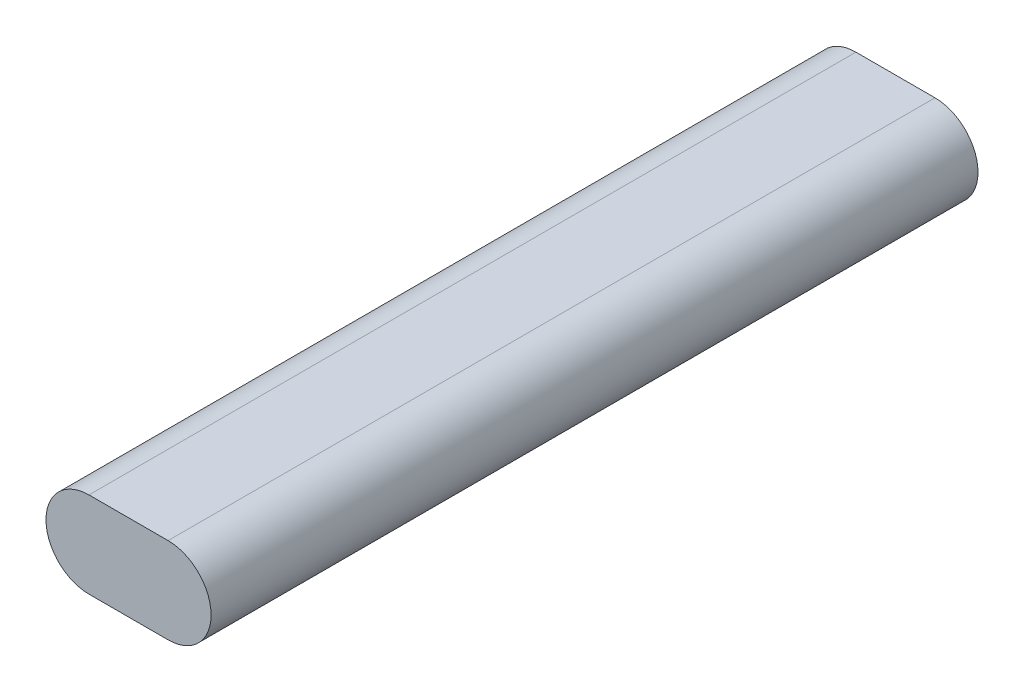
SolidWorks part; units mm, degrees
ref_plane "Front Plane" through (0, 0, 0) normal (0, 0, 1) x (1, 0, 0)
ref_plane "Top Plane" through (0, 0, 0) normal (0, 1, 0) x (1, 0, 0)
ref_plane "Right Plane" through (0, 0, 0) normal (1, 0, 0) x (0, 0, -1)
sketch "Sketch1" plane through (0, 0, 0) normal (0, 0, 1) x (1, 0, 0)
  line L0 (-11.5, 0) -> (11.5, 0) construction
  line L5 (-11.5, 12.5) -> (11.5, 12.5)
  line L6 (-11.5, -12.5) -> (11.5, -12.5)
  arc A0 (-11.5, 12.5) -> (-11.5, -12.5) centre (-11.5, 0) ccw
  arc A1 (11.5, -12.5) -> (11.5, 12.5) centre (11.5, 0) ccw
  point P2 (0, 0)
  point P9 (0, 0)
  point P10 (-24, 0)
  point P11 (24, 0)
  dimension "D1" = 25
  dimension "D2" = 48
extrude "Boss-Extrude1" add sketch "Sketch1" along normal blind 223
